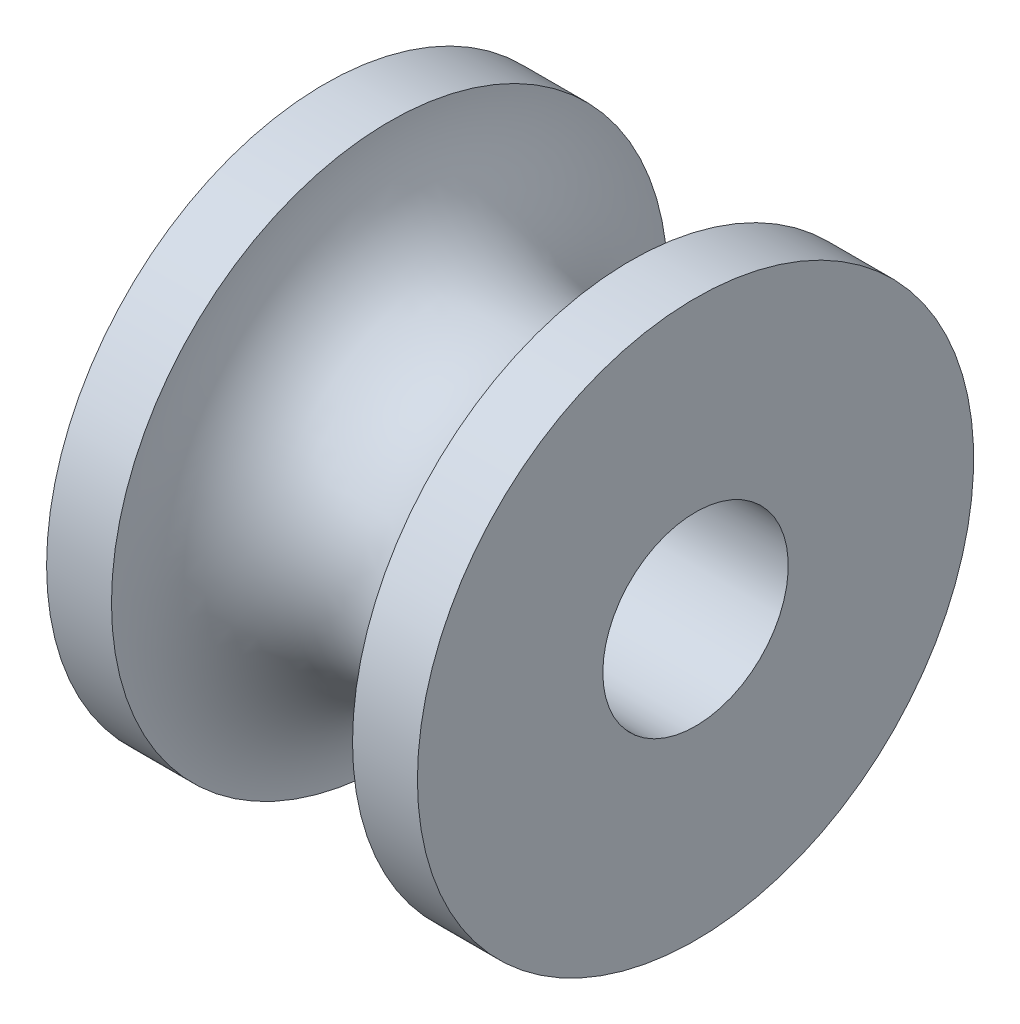
SolidWorks part; units mm, degrees
ref_plane "Plan de face" through (0, 0, 0) normal (0, 0, 1) x (1, 0, 0)
ref_plane "Plan de dessus" through (0, 0, 0) normal (0, 1, 0) x (1, 0, 0)
ref_plane "Plan de droite" through (0, 0, 0) normal (1, 0, 0) x (0, 0, -1)
sketch "Esquisse2" plane through (0, 0, 0) normal (0, 0, 1) x (1, 0, 0)
  line L0 (-4, -6) -> (-2.6, -6)
  line L1 (-4, -2) -> (4, -2)
  line L2 (-4, -2) -> (-4, -6)
  line L3 (-4, -6) -> (4, -6) construction
  line L4 (4, -2) -> (4, -6)
  line L5 (4, -6) -> (2.6, -6)
  line L6 (-9.5995, 0) -> (21.5663, 0) construction
  line L7 (0, -6) -> (0, 0) construction
  arc A0 (-2.6, -6) -> (2.6, -6) centre (0, -6) cw
  point P7 (-9.5995, 0)
  dimension "D1" = 4
  dimension "D2" = 2.6
  dimension "D3" = 8
  dimension "D4" = 2
revolve "Révolution1" add sketch "Esquisse2" angle 360 about L6
